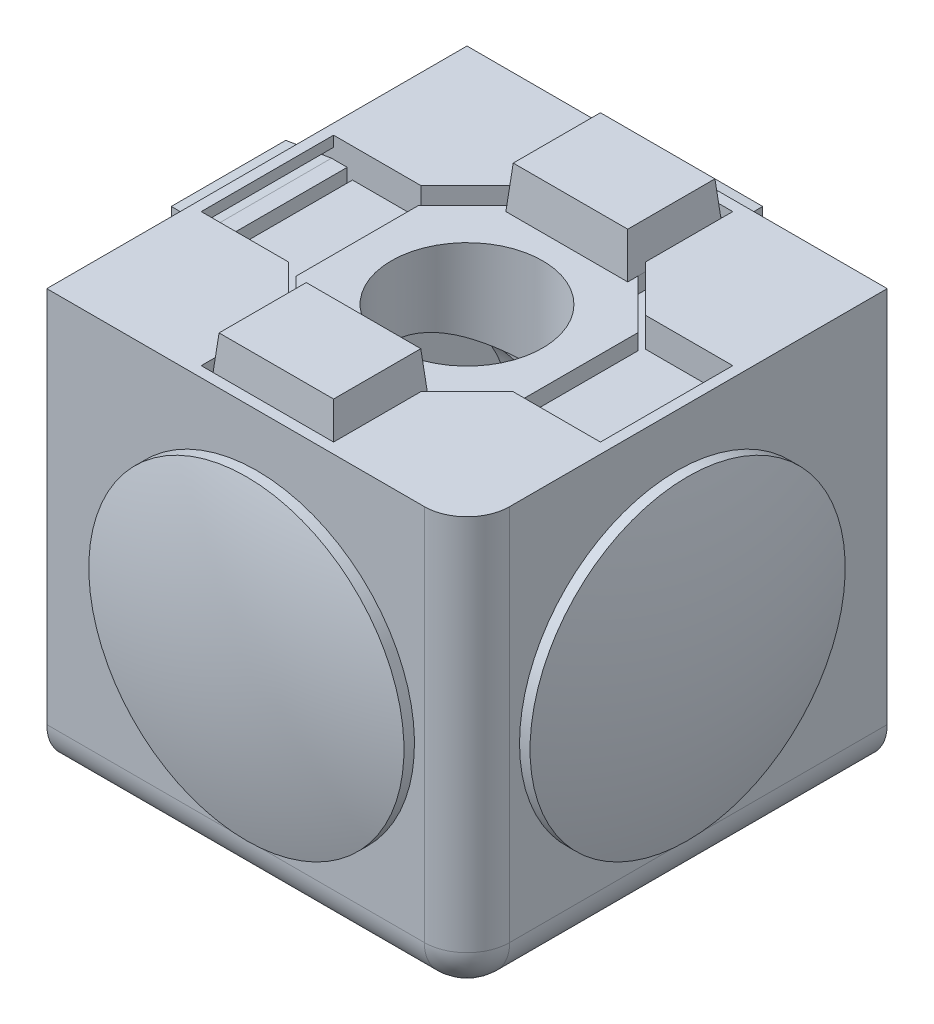
SolidWorks part; units mm, degrees
ref_plane "Front Plane" through (0, 0, 0) normal (0, 0, 1) x (1, 0, 0)
ref_plane "Top Plane" through (0, 0, 0) normal (0, 1, 0) x (1, 0, 0)
ref_plane "Right Plane" through (0, 0, 0) normal (1, 0, 0) x (0, 0, -1)
sketch "Sketch1" plane through (0, 0, 0) normal (0, 0, 1) x (1, 0, 0)
  line L0 (-10, -10) -> (10, 10) construction
  line L1 (-10, 10) -> (10, 10)
  line L2 (-10, 10) -> (-10, -10)
  line L3 (-10, -10) -> (10, -10)
  line L4 (10, 10) -> (10, -10)
  dimension "D1" = 20
extrude "Extrude1" add sketch "Sketch1" along normal mid plane 20
sketch "Sketch2" plane through (0, 0, 10) normal (0, 0, 1) x (1, 0, 0)
  circle A0 centre (0, 0) radius 6
  dimension "D1" = 12
extrude "Cut-Extrude1" cut sketch "Sketch2" against normal through all
sketch "Sketch3" plane through (0, 0, 10) normal (0, 0, 1) x (1, 0, 0)
  circle A0 centre (0, 0) radius 7.05
  dimension "D1" = 14.1
extrude "Cut-Extrude2" cut sketch "Sketch3" against normal through all draft 45
sketch "Sketch4" plane through (0, 0, -10) normal (0, 0, -1) x (-1, 0, 0)
  circle A0 centre (0, 0) radius 3.6
  circle A1 centre (0, 0) radius 6 construction
  circle A2 centre (0, 0) radius 6
  dimension "D1" = 7.2
extrude "Extrude2" add sketch "Sketch4" against normal blind 6
sketch "Sketch14" plane through (0, 0, -10) normal (0, 0, -1) x (-1, 0, 0)
  line L0 (-3.15, 5.3353) -> (-5.3353, 3.15)
  line L1 (-3.15, 9.5) -> (3.15, 9.5)
  line L2 (-3.15, 9.5) -> (-3.15, 5.3353)
  line L3 (-3.15, -9.5) -> (3.15, -9.5)
  line L4 (3.15, 9.5) -> (3.15, 5.3353)
  line L5 (-9.5, 3.15) -> (-5.3353, 3.15)
  line L6 (-9.5, 3.15) -> (-9.5, -3.15)
  line L7 (-9.5, -3.15) -> (-5.3353, -3.15)
  line L8 (9.5, 3.15) -> (9.5, -3.15)
  line L9 (3.15, 5.3353) -> (5.3353, 3.15)
  line L10 (-5.3353, -3.15) -> (-3.15, -5.3353)
  line L11 (5.3353, -3.15) -> (3.15, -5.3353)
  line L12 (-3.15, -5.3353) -> (-3.15, -9.5)
  line L13 (0, 0) -> (-9.5, 0) construction
  line L14 (3.15, -5.3353) -> (3.15, -9.5)
  line L15 (5.3353, -3.15) -> (9.5, -3.15)
  line L16 (5.3353, 3.15) -> (9.5, 3.15)
  line L17 (0, 0) -> (0, 9.5) construction
  dimension "D1" = 6.3
  dimension "D2" = 12
  dimension "D4" = 19
extrude "Cut-Extrude7" cut sketch "Sketch14" against normal blind 1.4
sketch "Sketch15" plane through (0, 0, -8.6) normal (0, 0, -1) x (-1, 0, 0)
  line L16 (-5.2317, 2.9) -> (-5.2317, -2.9)
  line L17 (5.2317, -2.9) -> (5.2317, 2.9)
  line L32 (-2.9, 9.25) -> (-2.9, 5.2317)
  line L33 (-2.9, 5.2317) -> (-5.2317, 2.9)
  line L34 (-5.2317, 2.9) -> (-9.25, 2.9)
  line L35 (-9.25, 2.9) -> (-9.25, -2.9)
  line L36 (-9.25, -2.9) -> (-5.2317, -2.9)
  line L37 (-5.2317, -2.9) -> (-2.9, -5.2317)
  line L38 (-2.9, -5.2317) -> (-2.9, -9.25)
  line L39 (-2.9, -9.25) -> (2.9, -9.25)
  line L40 (2.9, -9.25) -> (2.9, -5.2317)
  line L41 (2.9, -5.2317) -> (5.2317, -2.9)
  line L42 (5.2317, -2.9) -> (9.25, -2.9)
  line L43 (9.25, -2.9) -> (9.25, 2.9)
  line L44 (9.25, 2.9) -> (5.2317, 2.9)
  line L45 (5.2317, 2.9) -> (2.9, 5.2317)
  line L46 (2.9, 5.2317) -> (2.9, 9.25)
  line L47 (2.9, 9.25) -> (-2.9, 9.25)
  line L48 (-2.9, 9.25) -> (-2.9, 5.2317)
  line L49 (-2.9, 5.2317) -> (-5.2317, 2.9)
  line L53 (-5.2317, -2.9) -> (-2.9, -5.2317)
  line L54 (-2.9, -5.2317) -> (-2.9, -9.25)
  line L55 (-2.9, -9.25) -> (2.9, -9.25)
  line L56 (2.9, -9.25) -> (2.9, -5.2317)
  line L57 (2.9, -5.2317) -> (5.2317, -2.9)
  line L61 (5.2317, 2.9) -> (2.9, 5.2317)
  line L62 (2.9, 5.2317) -> (2.9, 9.25)
  line L63 (2.9, 9.25) -> (-2.9, 9.25)
  circle A0 centre (0, 0) radius 3.6 construction
  circle A1 centre (0, 0) radius 3.6
  dimension "D1" = 0.25
extrude "Extrude4" add sketch "Sketch15" along normal blind 0.75
sketch "Sketch16" plane through (0, 0, -9.35) normal (0, 0, -1) x (-1, 0, 0)
  line L0 (2.9, 5.2317) -> (2.9, 9.25) construction
  line L1 (-2.9, 9.25) -> (2.9, 9.25)
  line L2 (-2.9, 9.25) -> (-2.9, 4.75)
  line L3 (-2.9, 4.75) -> (2.9, 4.75)
  line L4 (2.9, 9.25) -> (2.9, 4.75)
  line L5 (-2.9, -9.25) -> (2.9, -9.25)
  line L6 (-2.9, -9.25) -> (-2.9, -4.75)
  line L7 (-2.9, -4.75) -> (2.9, -4.75)
  line L8 (2.9, -9.25) -> (2.9, -4.75)
  dimension "D1" = 4.5
extrude "Extrude5" add sketch "Sketch16" along normal blind 2 draft 5
sketch "Sketch7" plane through (0, 0, 0) normal (0, 1, 0) x (1, 0, 0)
  line L0 (0, 0) -> (-10, 0) construction
  line L1 (-10, -10) -> (-10, 10) construction
ref_axis "Axis1" through (-10, 0, 0) along (1, 0, 0)
sketch "Sketch9" plane through (0, 0, 0) normal (0, 0, 1) x (1, 0, 0)
  line L0 (0, 0) -> (0, 11.5939) construction
ref_axis "Axis2" through (0, 11.5939, 0) along (0, -1, 0)
sketch "Sketch13" plane through (0, 0, 0) normal (1, 0, 0) x (0, 0, -1)
  line L0 (-10, -7.5) -> (-10, -6)
  line L1 (-10, -6) -> (-7, -6)
  line L2 (-7, -6) -> (-7, -5.5)
  line L3 (-7, -5.5) -> (-10, -5.5)
  line L4 (-10, -5.5) -> (-10, 0)
  line L5 (-10, 0) -> (-11.5, 0)
  line L6 (-10, -7.5) -> (-10.5, -7.5)
  line L7 (-10, -10) -> (-10, 10) construction
  line L8 (0, 0) -> (-10, 0) construction
  arc A0 (-10.5, -7.5) -> (-11.5, 0) centre (17.125, 0) cw
  dimension "D1" = 1.5
  dimension "D2" = 0.5
  dimension "D3" = 3
  dimension "D4" = 1.5
revolve "Revolve1" add sketch "Sketch13" angle 360 about L8
pattern_circular "CirPattern1" count 2 over 90 about axis through (0, 0, 0) along (1, 0, 0) of "Cut-Extrude1", "Cut-Extrude2", "Extrude2", "Revolve1", "Cut-Extrude7", "Extrude4", "Extrude5"
pattern_circular "CirPattern2" count 2 over 90 about axis through (0, 0, 0) along (0, 1, 0) of "Cut-Extrude1", "Cut-Extrude2", "Extrude2", "Revolve1", "Extrude5", "Extrude4", "Cut-Extrude7"
fillet "Fillet2" radius 2.032 3 edges at (0, -10, 10) (10, -10, 0) (10, 0, 10)
